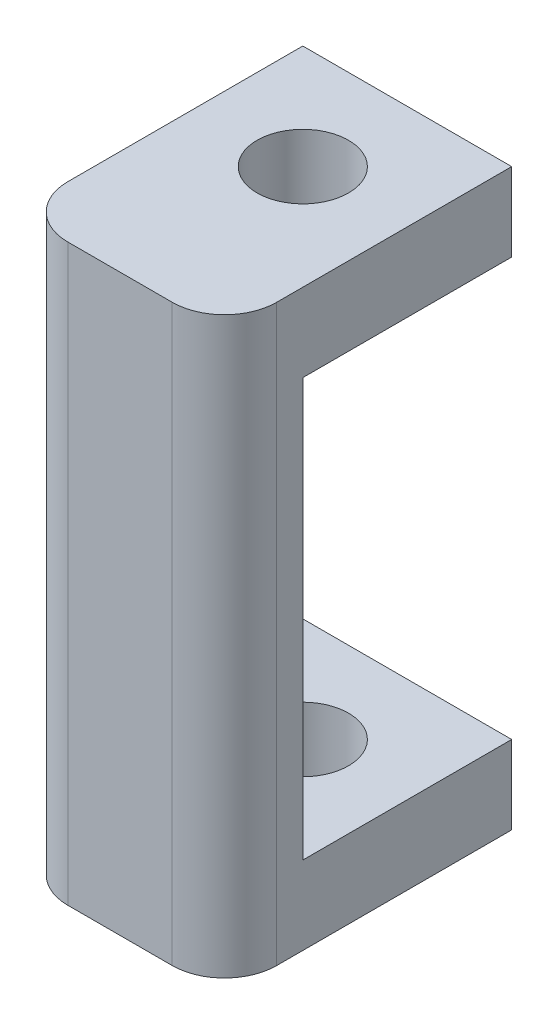
SolidWorks part; units mm, degrees
ref_plane "前视基准面" through (0, 0, 0) normal (0, 0, 1) x (1, 0, 0)
ref_plane "上视基准面" through (0, 0, 0) normal (0, 1, 0) x (1, 0, 0)
ref_plane "右视基准面" through (0, 0, 0) normal (1, 0, 0) x (0, 0, -1)
sketch "草图1" plane through (0, 0, 0) normal (0, 1, 0) x (1, 0, 0)
  line L0 (0, 0) -> (8, 0)
  line L1 (8, 0) -> (8, -8)
  line L2 (8, -8) -> (0, -8)
  line L3 (0, -8) -> (0, 0)
  line L4 (0, 0) -> (8, -8) construction
  line L5 (0, -8) -> (8, -8)
  line L6 (0, -8) -> (0, -9)
  line L7 (2, -11) -> (6, -11)
  line L8 (8, -8) -> (8, -9)
  circle A0 centre (4, -4) radius 1.75
  arc A1 (6, -11) -> (8, -9) centre (6, -9) ccw
  arc A2 (0, -9) -> (2, -11) centre (2, -9) ccw
  point P11 (8, -11)
  dimension "D4" = 3.5
  dimension "D5" = 2
  dimension "D1" = 8
  dimension "D2" = 8
  dimension "D3" = 3
extrude "凸台-拉伸1" add sketch "草图1" along normal blind 3 contours L4 L3 L2 A0 | L0 L4 A0 L1 | L6 A2 L7 A1 L8 L2
sketch "草图2" plane through (0, 3, 0) normal (0, 1, 0) x (1, 0, 0)
  line L0 (8, -8) -> (0, -8)
  line L1 (8, 0) -> (8, -9) construction
  line L2 (0, -9) -> (0, 0) construction
  line L3 (2, -11) -> (6, -11) construction
  line L4 (2, -11) -> (6, -11)
  line L5 (8, -8) -> (8, -9)
  line L6 (0, -8) -> (0, -9)
  arc A0 (6, -11) -> (8, -9) centre (6, -9) ccw construction
  arc A1 (0, -9) -> (2, -11) centre (2, -9) ccw construction
  arc A2 (6, -11) -> (8, -9) centre (6, -9) ccw
  arc A3 (0, -9) -> (2, -11) centre (2, -9) ccw
  dimension "D1" = 3
extrude "凸台-拉伸2" add sketch "草图2" along normal blind 16
sketch "草图3" plane through (0, 19, 0) normal (0, 1, 0) x (1, 0, 0)
  line L0 (8, -9) -> (8, -8) construction
  line L1 (2, -11) -> (6, -11) construction
  line L2 (0, -8) -> (0, -9) construction
  line L3 (0, -8) -> (0, 0) construction
  line L4 (0, 0) -> (8, 0) construction
  line L5 (8, 0) -> (8, -8) construction
  line L6 (8, -9) -> (8, -8)
  line L7 (2, -11) -> (6, -11)
  line L8 (0, -8) -> (0, -9)
  line L9 (0, -8) -> (0, 0)
  line L10 (0, 0) -> (8, 0)
  line L11 (8, 0) -> (8, -8)
  circle A0 centre (4, -4) radius 1.75 construction
  arc A1 (6, -11) -> (8, -9) centre (6, -9) ccw construction
  arc A2 (0, -9) -> (2, -11) centre (2, -9) ccw construction
  circle A3 centre (4, -4) radius 1.75
  arc A4 (6, -11) -> (8, -9) centre (6, -9) ccw
  arc A5 (0, -9) -> (2, -11) centre (2, -9) ccw
extrude "凸台-拉伸3" add sketch "草图3" along normal blind 3
